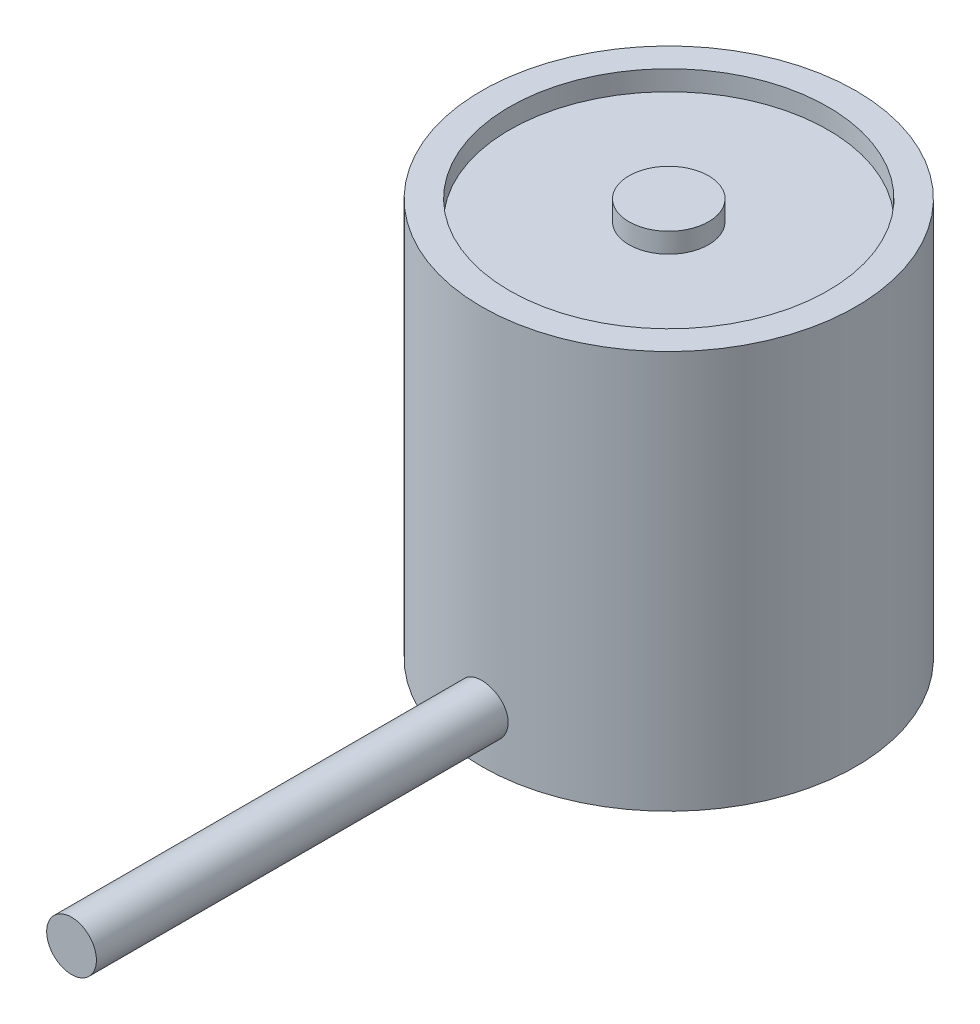
SolidWorks part; units mm, degrees
ref_plane "Front Plane" through (0, 0, 0) normal (0, 0, 1) x (1, 0, 0)
ref_plane "Top Plane" through (0, 0, 0) normal (0, 1, 0) x (1, 0, 0)
ref_plane "Right Plane" through (0, 0, 0) normal (1, 0, 0) x (0, 0, -1)
sketch "Sketch1" plane through (0, 0, 0) normal (0, 1, 0) x (1, 0, 0)
  circle A0 centre (0, 0) radius 11.938
  dimension "D1" = 23.876
extrude "Boss-Extrude1" add sketch "Sketch1" along normal blind 25.4
sketch "Sketch2" plane through (0, 25.4, 0) normal (0, 1, 0) x (1, 0, 0)
  circle A0 centre (0, 0) radius 2.54
  circle A1 centre (0, 0) radius 10.16
  dimension "D1" = 5.08
  dimension "D2" = 20.32
extrude "Cut-Extrude1" cut sketch "Sketch2" against normal blind 1.27
sketch "Sketch3" plane through (0, 0, 0) normal (0, 0, 1) x (1, 0, 0)
  circle A0 centre (0, 3.175) radius 1.5875
  dimension "D1" = 3.175
  dimension "D2" = 3.175
extrude "Boss-Extrude2" add sketch "Sketch3" along normal blind 38.1
